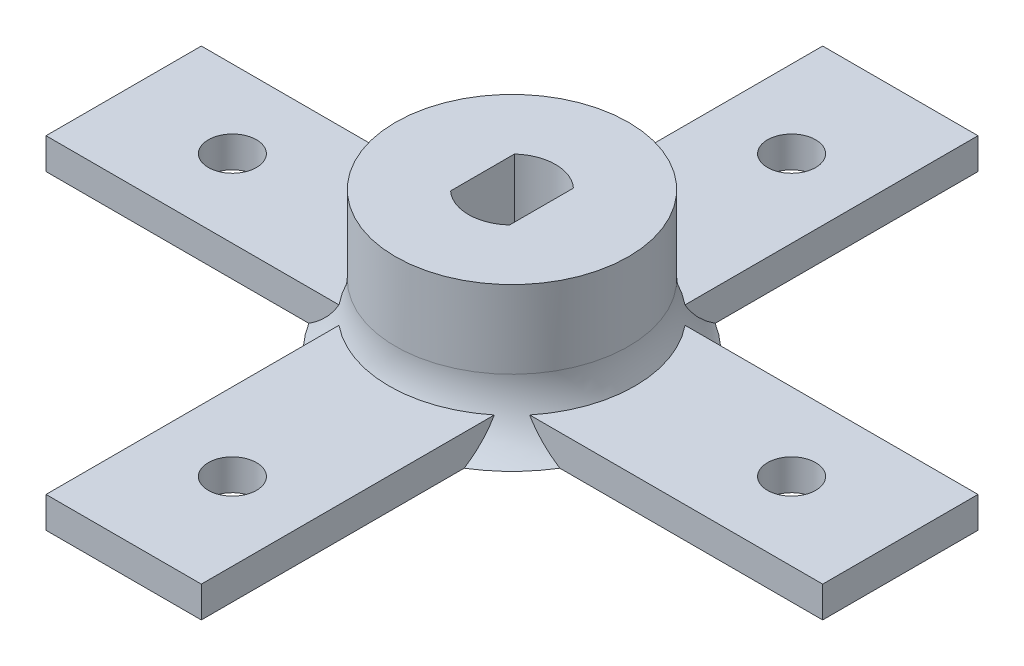
SolidWorks part; units mm, degrees
ref_plane "Alzado" through (0, 0, 0) normal (0, 0, 1) x (1, 0, 0)
ref_plane "Planta" through (0, 0, 0) normal (0, 1, 0) x (1, 0, 0)
ref_plane "Vista lateral" through (0, 0, 0) normal (1, 0, 0) x (0, 0, -1)
sketch "Croquis1" plane through (0, 0, 0) normal (0, 1, 0) x (1, 0, 0)
  circle A0 centre (0, 0) radius 7.5
  dimension "D1" = 15
extrude "Extruir1" add sketch "Croquis1" along normal blind 10
sketch "Croquis2" plane through (0, 10, 0) normal (0, 1, 0) x (1, 0, 0)
  line L2 (-1.9, 2.0567) -> (-1.9, -2.0567)
  line L4 (1.9, 2.0567) -> (1.9, -2.0567)
  arc A0 (-1.9, -2.0567) -> (1.9, -2.0567) centre (0, 0) ccw
  arc A1 (1.9, 2.0567) -> (-1.9, 2.0567) centre (0, 0) ccw
  dimension "D1" = 5.6
  dimension "D2" = 3.8
  dimension "D3" = 1.9
extrude "Extruir2" cut sketch "Croquis2" against normal blind 10
sketch "Croquis3" plane through (0, 0, 0) normal (0, -1, 0) x (1, 0, 0)
  circle A0 centre (0, 0) radius 30
  dimension "D1" = 60
extrude "Extruir3" add sketch "Croquis3" along normal blind 9
fillet "Redondeo1" radius 5 1 edges at (0, 0, -7.5)
sketch "Croquis4" plane through (0, 0, 0) normal (0, 1, 0) x (1, 0, 0)
  line L0 (0, -39.0705) -> (0, 51.8956) construction
  line L1 (-40.5115, 0) -> (62.1652, 0) construction
  arc A0 (-13.8964, -5.6471) -> (-5.6471, -13.8964) centre (0, 0) ccw
  arc A1 (-25.4768, -10.3529) -> (-10.3529, -25.4768) centre (0, 0) ccw
  circle A2 centre (0, 0) radius 21.25 construction
  arc A3 (-5.6471, 13.8964) -> (-10.3529, 25.4768) centre (-8, 19.6866) ccw
  arc A4 (10.3529, 25.4768) -> (5.6471, 13.8964) centre (8, 19.6866) ccw
  arc A5 (-25.4768, 10.3529) -> (-13.8964, 5.6471) centre (-19.6866, 8) ccw
  arc A6 (13.8964, 5.6471) -> (25.4768, 10.3529) centre (19.6866, 8) ccw
  arc A7 (-13.8964, -5.6471) -> (-25.4768, -10.3529) centre (-19.6866, -8) ccw
  arc A8 (-10.3529, -25.4768) -> (-5.6471, -13.8964) centre (-8, -19.6866) ccw
  arc A9 (5.6471, -13.8964) -> (10.3529, -25.4768) centre (8, -19.6866) ccw
  arc A10 (25.4768, -10.3529) -> (13.8964, -5.6471) centre (19.6866, -8) ccw
  arc A11 (10.3529, -25.4768) -> (25.4768, -10.3529) centre (0, 0) ccw
  arc A12 (5.6471, -13.8964) -> (13.8964, -5.6471) centre (0, 0) ccw
  arc A13 (13.8964, 5.6471) -> (5.6471, 13.8964) centre (0, 0) ccw
  arc A14 (25.4768, 10.3529) -> (10.3529, 25.4768) centre (0, 0) ccw
  arc A15 (-10.3529, 25.4768) -> (-25.4768, 10.3529) centre (0, 0) ccw
  arc A16 (-5.6471, 13.8964) -> (-13.8964, 5.6471) centre (0, 0) ccw
  dimension "D1" = 30
  dimension "D2" = 55
  dimension "D3" = 42.5
  dimension "D4" = 8
  dimension "D5" = 8
  dimension "D6" = 8
  dimension "D7" = 8
  dimension "D8" = 8
  dimension "D9" = 8
  dimension "D10" = 8
  dimension "D11" = 8
extrude "Extruir4" cut sketch "Croquis4" against normal blind 10
fillet "Redondeo2" radius 2 2 edges at (0, 0, -30) (0, -9, -30)
sketch "Croquis5" plane through (0, -9, 0) normal (0, -1, 0) x (1, 0, 0)
  circle A0 centre (0, 0) radius 39.8777
extrude "Cortar-Extruir1" cut sketch "Croquis5" against normal blind 10
sketch "Croquis7" plane through (0, 1, 0) normal (0, -1, 0) x (1, 0, 0)
  line L1 (-5, 25) -> (5, 25)
  line L2 (-5, 25) -> (-5, -25)
  line L3 (-5, -25) -> (5, -25)
  line L4 (5, 25) -> (5, -25)
  line L5 (-5, 25) -> (5, -25) construction
  line L6 (-5, -25) -> (5, 25) construction
  point P0 (0, 0)
  dimension "D1" = 50
  dimension "D2" = 10
extrude "Saliente-Extruir1" add sketch "Croquis7" against normal blind 2
sketch "Croquis8" plane through (0, 1, 0) normal (0, -1, 0) x (1, 0, 0)
  line L1 (-25, -5) -> (25, -5)
  line L2 (-25, -5) -> (-25, 5)
  line L3 (-25, 5) -> (25, 5)
  line L4 (25, -5) -> (25, 5)
  line L5 (-25, -5) -> (25, 5) construction
  line L6 (-25, 5) -> (25, -5) construction
  point P0 (0, 0)
  dimension "D1" = 50
  dimension "D2" = 10
extrude "Saliente-Extruir2" add sketch "Croquis8" against normal blind 2
sketch "Croquis10" plane through (0, 1, 0) normal (0, -1, 0) x (1, 0, 0)
  circle A0 centre (-18, 0) radius 1.55
  circle A1 centre (0, 18) radius 1.55
  circle A2 centre (0, -18) radius 1.55
  circle A3 centre (18, 0) radius 1.55
  dimension "D1" = 3.1
  dimension "D2" = 3.1
  dimension "D3" = 3.1
  dimension "D4" = 3.1
  dimension "D5" = 18
  dimension "D6" = 18
  dimension "D7" = 18
extrude "Cortar-Extruir2" cut sketch "Croquis10" against normal blind 2
